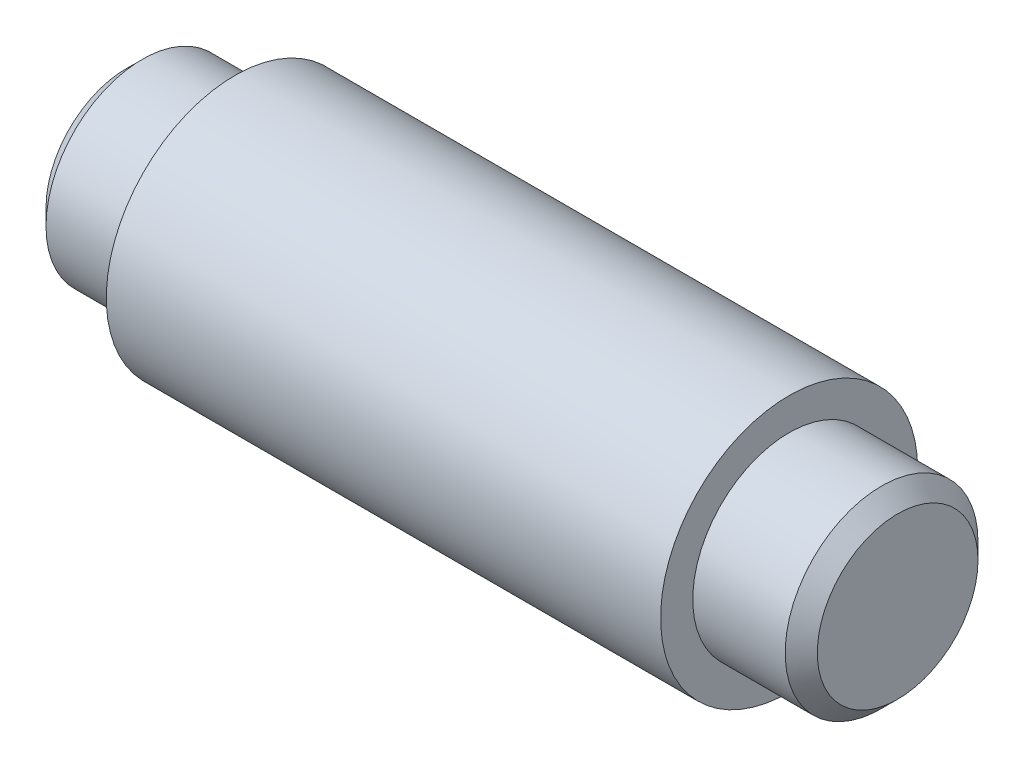
SolidWorks part; units mm, degrees
material "Alloy Steel"
ref_plane "Front Plane" through (0, 0, 0) normal (0, 0, 1) x (1, 0, 0)
ref_plane "Top Plane" through (0, 0, 0) normal (0, 1, 0) x (1, 0, 0)
ref_plane "Right Plane" through (0, 0, 0) normal (1, 0, 0) x (0, 0, -1)
sketch "Sketch1" plane through (0, 0, 0) normal (0, 0, 1) x (1, 0, 0)
  line L0 (0, 0) -> (0, 9.525)
  line L2 (0, 9.525) -> (10.7188, 9.525)
  line L3 (10.7188, 9.525) -> (10.7188, 12.7)
  line L4 (10.7188, 12.7) -> (65.4812, 12.7)
  line L5 (65.4812, 12.7) -> (65.4812, 9.525)
  line L6 (65.4812, 9.525) -> (76.2, 9.525)
  line L8 (76.2, 9.525) -> (76.2, 0)
  line L9 (76.2, 0) -> (0, 0)
  point P2 (76.2, 9.525)
  point P4 (0, 0)
  point P11 (0, 9.525)
  point P13 (0, 9.9538)
  dimension "D1" = 76.2
  dimension "D2" = 54.7624
  dimension "D3" = 12.7
  dimension "D4" = 9.525
  dimension "D5" = 9.525
  dimension "D10" = 10.7188
revolve "Revolve1" add sketch "Sketch1" angle 360 about L9
chamfer "Chamfer1" distance 1.5875 angle 45 1 edges at (76.2, 0, -9.525)
chamfer "Chamfer2" distance 1.5875 angle 45 1 edges at (0, 0, -9.525)
